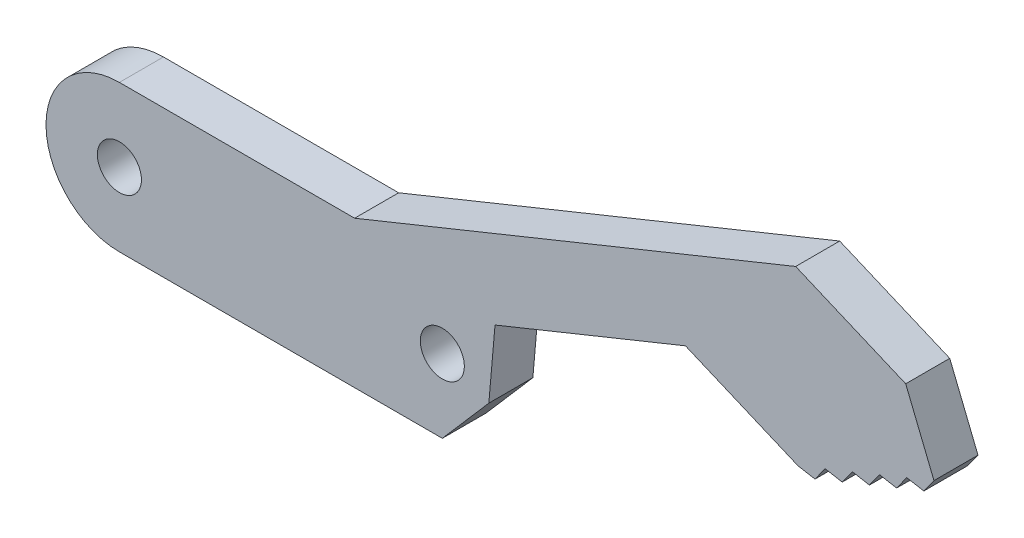
SolidWorks part; units mm, degrees
ref_plane "Front Plane" through (0, 0, 0) normal (0, 0, 1) x (1, 0, 0)
ref_plane "Top Plane" through (0, 0, 0) normal (0, 1, 0) x (1, 0, 0)
ref_plane "Right Plane" through (0, 0, 0) normal (1, 0, 0) x (0, 0, -1)
sketch "Sketch2" plane through (0, 0, 0) normal (0, 0, 1) x (1, 0, 0)
  line L1 (11, 5) -> (-11, 5)
  line L2 (11, 5) -> (11, -5) construction
  line L3 (11, -5) -> (-11, -5)
  line L4 (-11, 5) -> (-11, -5) construction
  line L5 (11, 5) -> (-11, -5) construction
  line L6 (11, -5) -> (-11, 5) construction
  arc A0 (-11, 5) -> (-11, -5) centre (-11, 0) ccw
  circle A1 centre (-11, 0) radius 1.5
  arc A2 (11, -5) -> (11, 5) centre (11, 0) ccw
  circle A3 centre (11, 0) radius 1.5
  point P0 (0, 0)
  dimension "D3" = 3
  dimension "D4" = 3
  dimension "D1" = 22
  dimension "D2" = 10
extrude "Boss-Extrude1" add sketch "Sketch2" along normal blind 3
sketch "Sketch3" plane through (0, 0, 3) normal (0, 0, 1) x (1, 0, 0)
  line L0 (11, -5) -> (44.7293, 8.6686) construction
  line L1 (-11, -5) -> (11, -5) construction
  line L2 (44.7293, 8.6686) -> (35.4614, 4.9129)
  line L3 (44.7293, 8.6686) -> (40.4058, 19.3377)
  line L4 (40.4058, 19.3377) -> (5.0254, 5)
  line L5 (11, 5) -> (-11, 5) construction
  line L6 (35.4614, 4.9129) -> (35.2248, 5.4967)
  line L7 (27.5645, 8.7389) -> (14.5894, 3.4808)
  line L8 (14.5894, 3.4808) -> (11, -5) construction
  line L9 (35.2248, 5.4967) -> (27.5645, 8.7389)
  line L10 (11, 5) -> (5.0254, 5)
  arc A0 (11, -5) -> (11, 5) centre (11, 0) ccw construction
  arc A2 (14.5894, 3.4808) -> (11, 5) centre (11, 0) ccw
  dimension "D1" = 157.94
  dimension "D3" = 10
  dimension "D5" = 90
  dimension "D6" = 14
  dimension "D7" = 0.63
  dimension "D8" = 5
  dimension "D9" = 45
  dimension "D10" = 45
extrude "Boss-Extrude2" add sketch "Sketch3" against normal blind 3 contours L4 L10 A2 L7 L9 L6 L2 L3
sketch "Sketch5" plane through (0, 0, 3) normal (0, 0, 1) x (1, 0, 0)
  line L0 (40.4058, 19.3377) -> (42.5675, 14.0032)
  line L1 (44.7293, 8.6686) -> (40.4058, 19.3377) construction
  line L2 (40.4058, 19.3377) -> (35.0712, 17.1759)
  line L3 (40.4058, 19.3377) -> (5.0254, 5) construction
  line L4 (35.0712, 17.1759) -> (42.5675, 14.0032)
  line L5 (35.2248, 5.4967) -> (27.5645, 8.7389) construction
extrude "Cut-Extrude1" cut sketch "Sketch5" against normal blind 3
sketch "Sketch6" plane through (0, 0, 3) normal (0, 0, 1) x (1, 0, 0)
  line L2 (11.7247, -0.4618) -> (12.1143, -0.4618)
  line L3 (35.2248, 5.4967) -> (44.4927, 9.2525) construction
  line L4 (35.2248, 5.4967) -> (36.3882, 5.2884)
  line L5 (36.3882, 5.2884) -> (37.0784, 6.2479)
  line L6 (37.0784, 6.2479) -> (38.2418, 6.0396)
  line L7 (38.2418, 6.0396) -> (38.932, 6.9991)
  line L8 (38.932, 6.9991) -> (40.0954, 6.7908)
  line L9 (40.0954, 6.7908) -> (40.7856, 7.7502)
  line L10 (40.7856, 7.7502) -> (41.949, 7.5419)
  line L11 (41.949, 7.5419) -> (42.6391, 8.5014)
  line L12 (42.6391, 8.5014) -> (43.8025, 8.2931)
  line L13 (43.8025, 8.2931) -> (44.4927, 9.2525)
  line L14 (35.2248, 5.4967) -> (35.4614, 4.9129)
  line L15 (35.4614, 4.9129) -> (44.7293, 8.6686)
  line L16 (44.7293, 8.6686) -> (44.4927, 9.2525)
  line L17 (14.5894, 3.4808) -> (14.1679, -1.3408)
  line L18 (14.1679, -1.3408) -> (11, -5)
  line L22 (44.7293, 8.6686) -> (35.4614, 4.9129) construction
  line L23 (35.4614, 4.9129) -> (35.2248, 5.4967) construction
  line L24 (44.7293, 8.6686) -> (42.5675, 14.0032) construction
  arc A1 (11, -5) -> (14.5894, 3.4808) centre (11, 0) ccw construction
  arc A2 (11, -5) -> (14.5894, 3.4808) centre (11, 0) ccw
  line M29 (35.2248, 5.4967) -> (35.4614, 4.9129)
  line M30 (35.4614, 4.9129) -> (44.7293, 8.6686)
  line M31 (44.7293, 8.6686) -> (42.5675, 14.0032)
  dimension "D1" = 4.84
extrude "Cut-Extrude2" cut sketch "Sketch6" against normal through all and the other way through all contours L10 L9 M30 | L8 L7 M30 | L6 L5 M30 | L4 M29 M30 | L12 L11 M30 | L13 M30 M31 | A2 L17 L18
